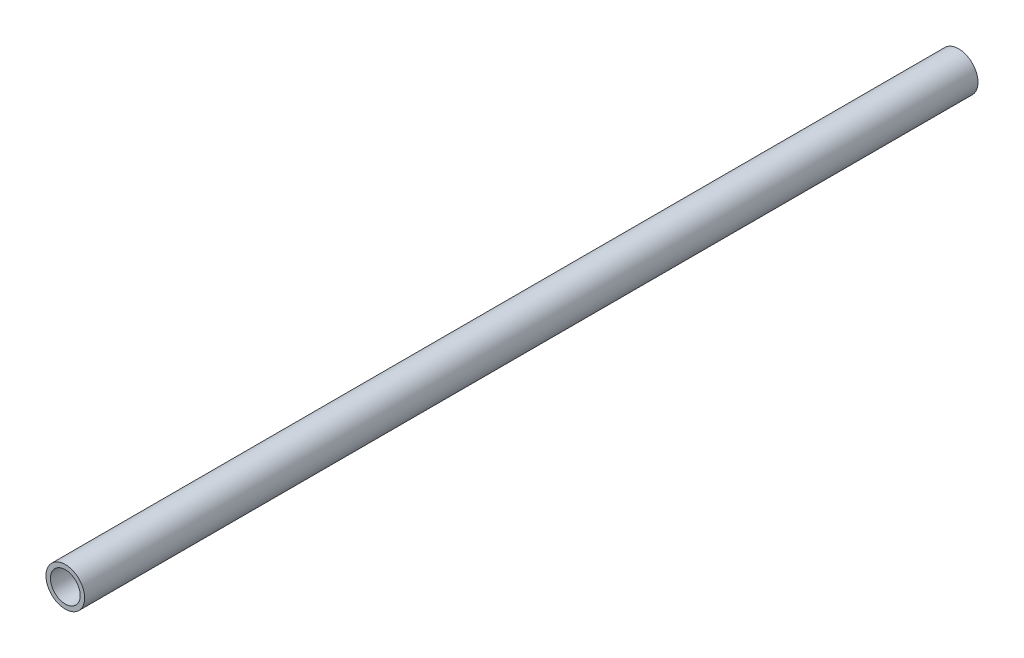
SolidWorks part; units mm, degrees
material "3.0255 (EN-AW 1350A)"
ref_plane "Alzado" through (0, 0, 0) normal (0, 0, 1) x (1, 0, 0)
ref_plane "Planta" through (0, 0, 0) normal (0, 1, 0) x (1, 0, 0)
ref_plane "Vista lateral" through (0, 0, 0) normal (1, 0, 0) x (0, 0, -1)
sketch "Croquis1" plane through (0, 0, 0) normal (0, 0, 1) x (1, 0, 0)
  circle A0 centre (0, 0) radius 5
  circle A1 centre (0, 0) radius 6.5
  dimension "D1" = 13
  dimension "D2" = 1.5
extrude "Saliente-Extruir1" add sketch "Croquis1" along normal mid plane 300
